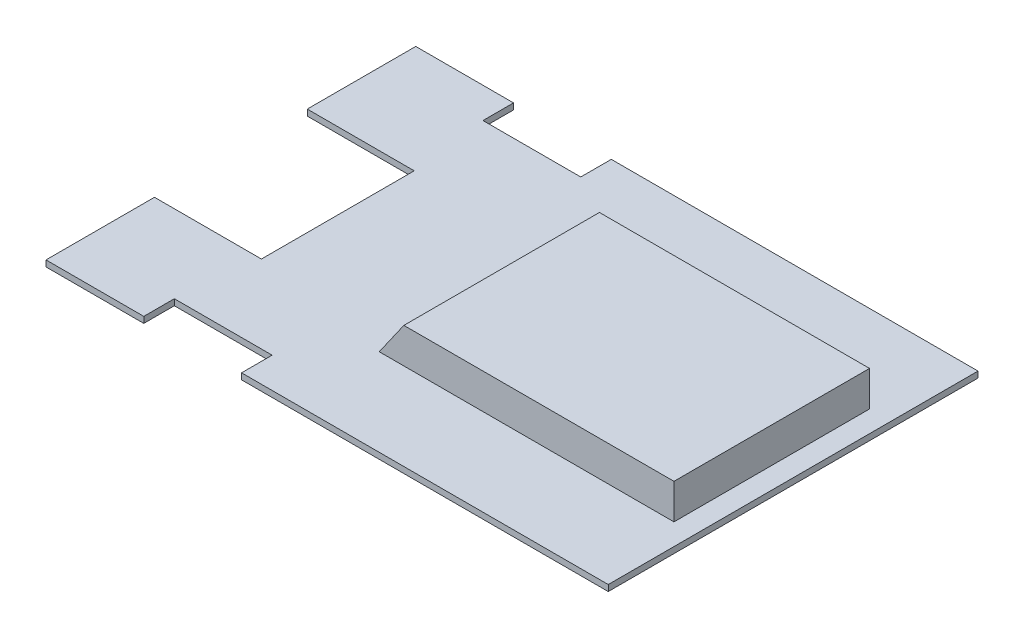
SolidWorks part; units mm, degrees
material "uhlíková ocel 7850"
ref_plane "Přední rovina" through (0, 0, 0) normal (0, 0, 1) x (1, 0, 0)
ref_plane "Horní rovina" through (0, 0, 0) normal (0, 1, 0) x (1, 0, 0)
ref_plane "Pravá rovina" through (0, 0, 0) normal (1, 0, 0) x (0, 0, -1)
sketch "Skica1" plane through (0, 0, 0) normal (0, 1, 0) x (1, 0, 0)
  line L1 (-92, -60.5) -> (92, -60.5)
  line L2 (-92, -60.5) -> (-92, 60.5)
  line L3 (-92, 60.5) -> (92, 60.5)
  line L4 (92, -60.5) -> (92, 60.5)
  line L5 (-92, -60.5) -> (92, 60.5) construction
  line L6 (-92, 60.5) -> (92, -60.5) construction
  point P0 (0, 0)
  dimension "D1" = 121
  dimension "D2" = 184
extrude "Přidat vysunutím1" add sketch "Skica1" along normal blind 2
sketch "Skica2" plane through (0, 2, 0) normal (0, 1, 0) x (1, 0, 0)
  line L1 (-60, 60.5) -> (-28, 60.5)
  line L2 (-60, 60.5) -> (-60, 50.5)
  line L3 (-60, 50.5) -> (-28, 50.5)
  line L4 (-28, 60.5) -> (-28, 50.5)
  line L5 (-92, 60.5) -> (-92, -60.5) construction
  line L6 (-92, 0) -> (0, 0) construction
  line L7 (-28, -60.5) -> (-28, -50.5)
  line L8 (-60, -50.5) -> (-28, -50.5)
  line L9 (-60, -60.5) -> (-60, -50.5)
  line L10 (-60, -60.5) -> (-28, -60.5)
  line L11 (92, 60.5) -> (-92, 60.5) construction
  dimension "D1" = 32
  dimension "D2" = 32
  dimension "D3" = 10
extrude "Odebrat vysunutím1" cut sketch "Skica2" against normal blind 3
sketch "Skica3" plane through (0, 2, 0) normal (0, 1, 0) x (1, 0, 0)
  line L1 (-92, -25) -> (-57, -25)
  line L2 (-92, -25) -> (-92, 25)
  line L3 (-57, 25) -> (-92, 25)
  line L4 (-57, -25) -> (-57, 25)
  line L7 (-92, -60.5) -> (-60, -60.5) construction
  line L8 (-60, 60.5) -> (-92, 60.5) construction
  line L9 (-92, 60.5) -> (-92, -60.5) construction
  dimension "D1" = 35.5
  dimension "D2" = 35.5
  dimension "D3" = 35
extrude "Odebrat vysunutím2" cut sketch "Skica3" against normal blind 10
sketch "Skica5" plane through (0, 2, 0) normal (0, 1, 0) x (1, 0, 0)
  line L0 (-92, 0) -> (0, 0) construction
  line L1 (-7, -30) -> (83, -30)
  line L2 (-7, -30) -> (-7, 30)
  line L3 (-7, 30) -> (83, 30)
  line L4 (83, -30) -> (83, 30)
  line L5 (-7, -30) -> (83, 30) construction
  line L6 (-7, 30) -> (83, -30) construction
  line L7 (-57, -25) -> (-57, 25) construction
  point P0 (38, 0)
  dimension "D1" = 60
  dimension "D2" = 90
  dimension "D3" = 50
extrude "Odebrat vysunutím3" cut sketch "Skica5" against normal blind 10
sketch "Skica6" plane through (0, 2, 0) normal (0, 1, 0) x (1, 0, 0)
  line L1 (-7, 30) -> (83, 30)
  line L2 (-7, 30) -> (-7, -30)
  line L3 (-7, -30) -> (83, -30)
  line L4 (83, 30) -> (83, -30)
  line L5 (-9, 32) -> (85, 32)
  line L6 (-9, 32) -> (-9, -32)
  line L7 (-9, -32) -> (85, -32)
  line L8 (85, 32) -> (85, -32)
  dimension "D1" = 2
  dimension "D2" = 2
  dimension "D3" = 2
  dimension "D4" = 2
extrude "Přidat vysunutím2" add sketch "Skica6" along normal blind 10
sketch "Skica7" plane through (0, 0, 32) normal (0, 0, 1) x (1, 0, 0)
  line L0 (-9, 2) -> (-1.9979, 12)
  line L1 (-9, 12) -> (85, 12) construction
  line L2 (-1.9979, 12) -> (-9, 12)
  line L3 (-9, 12) -> (-9, 2)
  line L4 (-92, 2) -> (0, 2) construction
  dimension "D1" = 55
extrude "Odebrat vysunutím4" cut sketch "Skica7" against normal through all
sketch "Skica8" plane through (0, 0, 32) normal (0, 0, 1) x (1, 0, 0)
  line L0 (-1.9979, 12) -> (-4.4395, 12)
  line L1 (-4.4395, 12) -> (-11.4415, 2)
  line L2 (-92, 2) -> (0, 2) construction
  line L3 (-11.4415, 2) -> (-9, 2)
  line L4 (-9, 2) -> (-1.9979, 12)
  dimension "D1" = 2
extrude "Přidat vysunutím3" add sketch "Skica8" against normal up to surface (64 mm away) up to face at (39.7505, 7, -32)
sketch "Skica9" plane through (0, 12, 0) normal (0, 1, 0) x (1, 0, 0)
  line L1 (-4.4395, 32) -> (85, 32)
  line L2 (-4.4395, 32) -> (-4.4395, -32)
  line L3 (-4.4395, -32) -> (85, -32)
  line L4 (85, 32) -> (85, -32)
extrude "Přidat vysunutím4" add sketch "Skica9" along normal blind 1.5
sketch "Skica10" plane through (0, 0, 32) normal (0, 0, 1) x (1, 0, 0)
  line L0 (-4.4395, 12) -> (-3.3892, 13.5)
  line L1 (-4.4395, 13.5) -> (85, 13.5) construction
  line L2 (-3.3892, 13.5) -> (-4.4395, 13.5)
  line L3 (-4.4395, 13.5) -> (-4.4395, 12)
  line L4 (-4.4395, 12) -> (-11.4415, 2) construction
extrude "Odebrat vysunutím5" cut sketch "Skica10" against normal through all
sketch "Skica11" plane through (0, 0, 0) normal (0, 0, 1) x (1, 0, 0)
  line L5 (83, 12) -> (-1.9979, 12)
  line L6 (-1.9979, 12) -> (-7, 4.8563)
  line L7 (-7, 4.8563) -> (-7, 0)
  line L8 (-7, 0) -> (83, 0)
  line L9 (83, 0) -> (83, 12)
  line L10 (83, 12) -> (-1.9979, 12)
  line L11 (-1.9979, 12) -> (-7, 4.8563)
  line L12 (-7, 4.8563) -> (-7, 0)
  line L13 (-7, 0) -> (83, 0)
  line L14 (83, 0) -> (83, 12)
  dimension "D1" = 0
extrude "Přidat vysunutím5" add sketch "Skica11" along normal mid plane 1.5
pattern_linear "LinPole1" count 2 spacing 15 along (0, 0, 1) count 2 spacing 15 along (0, 0, -1) of "Přidat vysunutím5"
sketch "Skica12" plane through (0, 0, 15.75) normal (0, 0, 1) x (1, 0, 0)
  line L0 (-28, 0) -> (92, 0) construction
  line L1 (8, 0) -> (9, 0)
  line L2 (8, 0) -> (8, 8)
  line L3 (8, 8) -> (9, 8)
  line L4 (9, 0) -> (9, 8)
  line L5 (-7, 0) -> (-7, 4.8563) construction
  line L6 (34, 0) -> (35, 0)
  line L7 (34, 0) -> (34, 8)
  line L8 (34, 8) -> (35, 8)
  line L9 (35, 0) -> (35, 8)
  line L10 (60, 0) -> (61, 0)
  line L11 (60, 0) -> (60, 8)
  line L12 (60, 8) -> (61, 8)
  line L13 (61, 0) -> (61, 8)
  dimension "D1" = 1
  dimension "D2" = 1
  dimension "D3" = 1
  dimension "D4" = 8
  dimension "D7" = 15
  dimension "D8" = 25
  dimension "D9" = 25
extrude "Odebrat vysunutím6" cut sketch "Skica12" against normal up to surface (31.5 mm away) up to face at (30.0004, 5.7713, -15.75)
